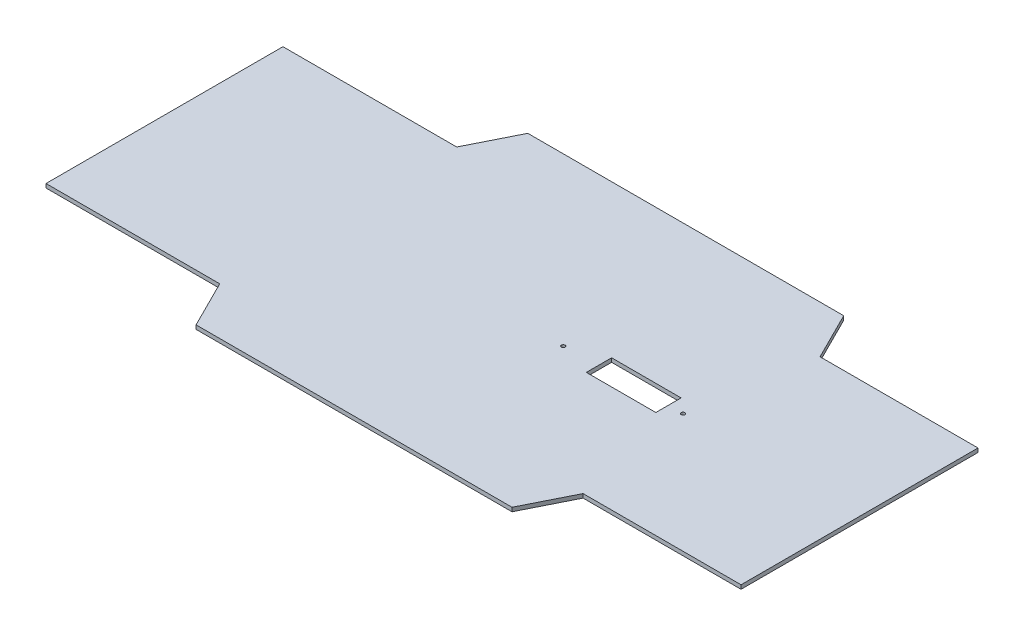
SolidWorks part; units mm, degrees
ref_plane "Front Plane" through (0, 0, 0) normal (0, 0, 1) x (1, 0, 0)
ref_plane "Top Plane" through (0, 0, 0) normal (0, 1, 0) x (1, 0, 0)
ref_plane "Right Plane" through (0, 0, 0) normal (1, 0, 0) x (0, 0, -1)
sketch "Sketch3" plane through (0, 0, 0) normal (0, 1, 0) x (1, 0, 0)
  line L0 (-279.4, 95.25) -> (-139.7, 95.25)
  line L1 (-279.4, -133.35) -> (279.4, -133.35) construction
  line L2 (-279.4, -133.35) -> (-279.4, 133.35) construction
  line L3 (-279.4, 133.35) -> (279.4, 133.35) construction
  line L4 (279.4, -133.35) -> (279.4, 133.35) construction
  line L5 (-279.4, -133.35) -> (279.4, 133.35) construction
  line L6 (-279.4, 133.35) -> (279.4, -133.35) construction
  line L7 (-279.4, -95.25) -> (279.4, -95.25) construction
  line L8 (-279.4, -95.25) -> (-279.4, 95.25) construction
  line L9 (-279.4, 95.25) -> (279.4, 95.25) construction
  line L10 (279.4, -95.25) -> (279.4, 95.25) construction
  line L13 (-139.7, 95.25) -> (-120.65, 133.35)
  line L14 (-120.65, 133.35) -> (133.35, 133.35)
  line L15 (133.35, 133.35) -> (152.4, 95.25)
  line L16 (152.4, 95.25) -> (279.4, 95.25)
  line L17 (-279.4, 95.25) -> (-279.4, -95.25)
  line L18 (279.4, 95.25) -> (279.4, -95.25)
  line L19 (-279.4, 0) -> (279.4, 0) construction
  line L20 (152.4, -95.25) -> (279.4, -95.25)
  line L21 (133.35, -133.35) -> (152.4, -95.25)
  line L22 (-120.65, -133.35) -> (133.35, -133.35)
  line L23 (-139.7, -95.25) -> (-120.65, -133.35)
  line L24 (-279.4, -95.25) -> (-139.7, -95.25)
  point P0 (0, 0)
  point P6 (0, 0)
  dimension "D1" = 266.7
  dimension "D2" = 558.8
  dimension "D3" = 190.5
  dimension "D4" = 127
  dimension "D5" = 139.7
  dimension "D6" = 254
extrude "Boss-Extrude1" add sketch "Sketch3" along normal mid plane 3.175
sketch "Sketch5" plane through (0, -1.5875, 0) normal (0, -1, 0) x (1, 0, 0)
  line L0 (-202.3532, 0) -> (279.4, 0) construction
  line L1 (-63.5, 25.4) -> (76.2, 25.4)
  line L2 (-63.5, 25.4) -> (-63.5, 88.9)
  line L3 (-63.5, 88.9) -> (76.2, 88.9)
  line L4 (76.2, 25.4) -> (76.2, 88.9)
  line L5 (-63.5, 25.4) -> (76.2, 88.9) construction
  line L6 (-63.5, 88.9) -> (76.2, 25.4) construction
  line L7 (279.4, 95.25) -> (279.4, -95.25) construction
  line L8 (-120.65, 133.35) -> (133.35, 133.35) construction
  line L9 (-120.65, 133.35) -> (133.35, 133.35) construction
  line L10 (6.35, 133.35) -> (6.35, 88.9) construction
  line L11 (-63.5, -88.9) -> (76.2, -88.9)
  line L12 (76.2, -25.4) -> (76.2, -88.9)
  line L13 (-63.5, -25.4) -> (76.2, -25.4)
  line L14 (-63.5, -25.4) -> (-63.5, -88.9)
  point P4 (6.35, 57.15)
  dimension "D1" = 63.5
  dimension "D2" = 139.7
  dimension "D3" = 44.45
sketch "Sketch6" plane through (0, 1.5875, 0) normal (0, 1, 0) x (1, 0, 0)
  line L0 (-279.4, 95.25) -> (-139.7, 95.25) construction
  line L1 (-120.65, 133.35) -> (-139.7, 95.25) construction
  line L2 (-139.7, 95.25) -> (-279.4, 95.25) construction
  line L3 (-139.7, 95.25) -> (-120.65, 133.35) construction
  line L4 (-120.65, 133.35) -> (133.35, 133.35) construction
  line L5 (133.35, 133.35) -> (152.4, 95.25) construction
  line L6 (152.4, 95.25) -> (279.4, 95.25) construction
  line L7 (279.4, 95.25) -> (279.4, -95.25) construction
  line L8 (279.4, -95.25) -> (152.4, -95.25) construction
  line L9 (133.35, -133.35) -> (152.4, -95.25) construction
  line L10 (152.4, -95.25) -> (279.4, -95.25) construction
  line L11 (152.4, -95.25) -> (133.35, -133.35) construction
  line L12 (133.35, -133.35) -> (-120.65, -133.35) construction
  line L13 (-120.65, -133.35) -> (-139.7, -95.25) construction
  line L14 (-139.7, -95.25) -> (-279.4, -95.25) construction
  line L15 (-279.4, -95.25) -> (-279.4, 95.25) construction
  line L16 (-276.225, 92.075) -> (-137.7377, 92.075)
  line L17 (-137.7377, 92.075) -> (-118.6877, 130.175)
  line L18 (-118.6877, 130.175) -> (131.3877, 130.175)
  line L19 (131.3877, 130.175) -> (150.4377, 92.075)
  line L20 (150.4377, 92.075) -> (276.225, 92.075)
  line L21 (276.225, 92.075) -> (276.225, -92.075)
  line L22 (276.225, -92.075) -> (150.4377, -92.075)
  line L23 (150.4377, -92.075) -> (131.3877, -130.175)
  line L24 (131.3877, -130.175) -> (-118.6877, -130.175)
  line L25 (-118.6877, -130.175) -> (-137.7377, -92.075)
  line L26 (-137.7377, -92.075) -> (-276.225, -92.075)
  line L27 (-276.225, -92.075) -> (-276.225, 92.075)
  dimension "D1" = 3.175
sketch "Sketch7" plane through (0, 1.5875, 0) normal (0, 1, 0) x (1, 0, 0)
  line L0 (279.4, 95.25) -> (279.4, -95.25) construction
  circle A0 centre (203.2, 0) radius 44.45
  dimension "D1" = 88.9
  dimension "D2" = 76.2
sketch "Sketch8" plane through (0, 1.5875, 0) normal (0, 1, 0) x (1, 0, 0)
  line L0 (138.4133, 0.5955) -> (125.2053, 0.5955) construction
  line L2 (69.3253, 10.7555) -> (125.2053, 10.7555)
  line L3 (69.3253, 10.7555) -> (69.3253, -9.5645)
  line L4 (69.3253, -9.5645) -> (125.2053, -9.5645)
  line L5 (125.2053, 10.7555) -> (125.2053, -9.5645)
  line L6 (69.3253, 10.7555) -> (125.2053, -9.5645) construction
  line L7 (69.3253, -9.5645) -> (125.2053, 10.7555) construction
  circle A0 centre (136.9147, 0.5955) radius 1.4986
  circle A1 centre (41.7845, -0.5955) radius 1.4899
  point P8 (0, 0)
  point P9 (97.2653, 0.5955)
  dimension "D2" = 2.9972
  dimension "D1" = 13.208
  dimension "D3" = 55.88
  dimension "D4" = 20.32
extrude "Cut-Extrude1" cut sketch "Sketch8" against normal blind 20.32
